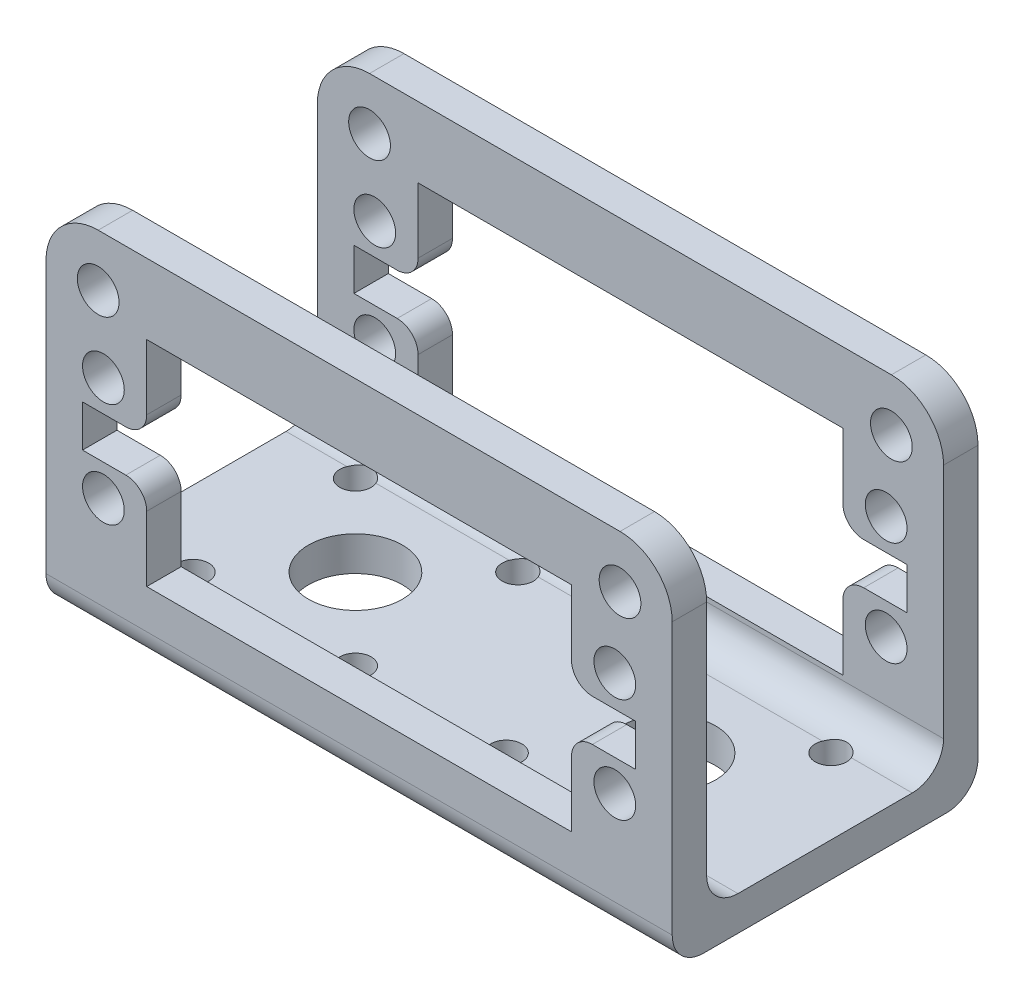
SolidWorks part; units mm, degrees
material "1060 Alloy"
ref_plane "Front Plane" through (0, 0, 0) normal (0, 0, 1) x (1, 0, 0)
ref_plane "Top Plane" through (0, 0, 0) normal (0, 1, 0) x (1, 0, 0)
ref_plane "Right Plane" through (0, 0, 0) normal (1, 0, 0) x (0, 0, -1)
sketch "Sketch1" plane through (0, 0, 0) normal (0, 0, 1) x (1, 0, 0)
  line L0 (-26.5, 0) -> (26.5, 0) construction
  line L1 (30, -17) -> (-30, -17)
  line L2 (30, -17) -> (30, 12)
  line L3 (25, 17) -> (-25, 17)
  line L4 (-30, -17) -> (-30, 12)
  line L5 (30, -17) -> (-30, 17) construction
  line L6 (30, 17) -> (-30, -17) construction
  line L7 (0, 10.25) -> (0, -10.25) construction
  line L8 (-20.35, -4) -> (-20.35, -10.25)
  line L9 (-20.35, 10.25) -> (20.35, 10.25)
  line L10 (-20.35, 10.25) -> (-20.35, 4)
  line L11 (-20.35, -10.25) -> (20.35, -10.25)
  line L12 (20.35, 10.25) -> (20.35, 4)
  line L13 (-20.35, 10.25) -> (20.35, -10.25) construction
  line L14 (-20.35, -10.25) -> (20.35, 10.25) construction
  line L15 (-26.5, 2) -> (-22.35, 2)
  line L16 (-26.5, 2) -> (-26.5, -2)
  line L17 (-26.5, -2) -> (-22.35, -2)
  line L18 (26.5, -2) -> (22.35, -2)
  line L19 (26.5, 2) -> (26.5, -2)
  line L20 (26.5, 2) -> (22.35, 2)
  line L21 (20.35, -4) -> (20.35, -10.25)
  arc A0 (30, 12) -> (25, 17) centre (25, 12) ccw
  arc A1 (-25, 17) -> (-30, 12) centre (-25, 12) ccw
  arc A2 (22.35, 2) -> (20.35, 4) centre (22.35, 4) cw
  arc A3 (22.35, -2) -> (20.35, -4) centre (22.35, -4) ccw
  arc A4 (-22.35, -2) -> (-20.35, -4) centre (-22.35, -4) cw
  arc A5 (-22.35, 2) -> (-20.35, 4) centre (-22.35, 4) ccw
  circle A6 centre (-24.5, 5) radius 2
  circle A7 centre (24.5, 5) radius 2
  circle A8 centre (24.5, -5) radius 2
  circle A9 centre (-24.5, -5) radius 2
  circle A10 centre (-25, 12) radius 2
  circle A11 centre (25, 12) radius 2
  point P0 (0, 0)
  point P16 (0, 0)
  point P25 (-26.5, 0)
  point P32 (20.35, 2)
  point P35 (20.35, -2)
  point P38 (-20.35, -2)
  point P41 (-20.35, 2)
  dimension "D3" = 5
  dimension "D8" = 2
  dimension "D9" = 4
  dimension "D12" = 4
  dimension "D1" = 60
  dimension "D2" = 34
  dimension "D4" = 40.7
  dimension "D5" = 20.5
  dimension "D6" = 4
  dimension "D7" = 6.15
  dimension "D10" = 10
  dimension "D11" = 49
extrude "Boss-Extrude1" add sketch "Sketch1" along normal blind 3.3
sketch "Sketch2" plane through (0, 0, 3.3) normal (0, 0, 1) x (1, 0, 0)
  line L0 (30, -17) -> (30, 12) construction
  line L1 (-30, -17) -> (30, -17)
  line L2 (-30, -17) -> (-30, -13.7)
  line L3 (-30, -13.7) -> (30, -13.7)
  line L4 (30, -17) -> (30, -13.7)
  dimension "D1" = 3.3
extrude "Boss-Extrude2" add sketch "Sketch2" against normal blind 26
sketch "Mirror Sketch" plane through (0, -13.7, 0) normal (0, 1, 0) x (1, 0, 0)
  line L0 (-30, 11.35) -> (30, 11.35) construction
  line L1 (-30, 22.7) -> (-30, 0) construction
  line L2 (30, 22.7) -> (30, 0) construction
ref_plane "Mirror_Plane" through (0, 0, -11.35) normal (0, 0, 1) x (1, 0, 0)
mirror "Mirror1" about plane through (0, 0, -11.35) normal (0, 0, 1) of "Boss-Extrude1"
fillet "Fillet1" radius 3 4 edges at (0, -13.7, 0) (0, -17, -26) (0, -17, 3.3)
sketch "Sketch4" plane through (0, -17, 0) normal (0, -1, 0) x (1, 0, 0)
  line L0 (-30, -11.35) -> (30, -11.35) construction
  line L1 (0, -23) -> (0, 0.3) construction
  line L2 (-30, -23) -> (30, -23) construction
  line L3 (30, 0.3) -> (-30, 0.3) construction
  line L4 (-15, -11.35) -> (-22.7782, -3.5718) construction
  line L5 (-15, -11.35) -> (-15, -0.35) construction
  line L6 (-15, -11.35) -> (-7.2218, -3.5718) construction
  line L7 (-26, -11.35) -> (-4, -11.35) construction
  line L8 (-15, -11.35) -> (-7.2218, -19.1282) construction
  line L9 (-15, -11.35) -> (-22.7782, -19.1282) construction
  circle A0 centre (-15, -11.35) radius 11 construction
  circle A1 centre (15, -11.35) radius 11 construction
  circle A2 centre (-22.7782, -3.5718) radius 1.5
  circle A3 centre (-7.2218, -3.5718) radius 1.5
  circle A4 centre (-7.2218, -19.1282) radius 1.5
  circle A5 centre (-22.7782, -19.1282) radius 1.5
  circle A6 centre (22.7782, -19.1282) radius 1.5
  circle A7 centre (7.2218, -19.1282) radius 1.5
  circle A8 centre (7.2218, -3.5718) radius 1.5
  circle A9 centre (22.7782, -3.5718) radius 1.5
  circle A10 centre (-15, -11.35) radius 4.5
  circle A11 centre (15, -11.35) radius 4.5
  dimension "D1" = 22
  dimension "D4" = 3
  dimension "D5" = 9
  dimension "D2" = 30
  dimension "D3" = 45
extrude "Cut-Extrude1" cut sketch "Sketch4" against normal blind 18
